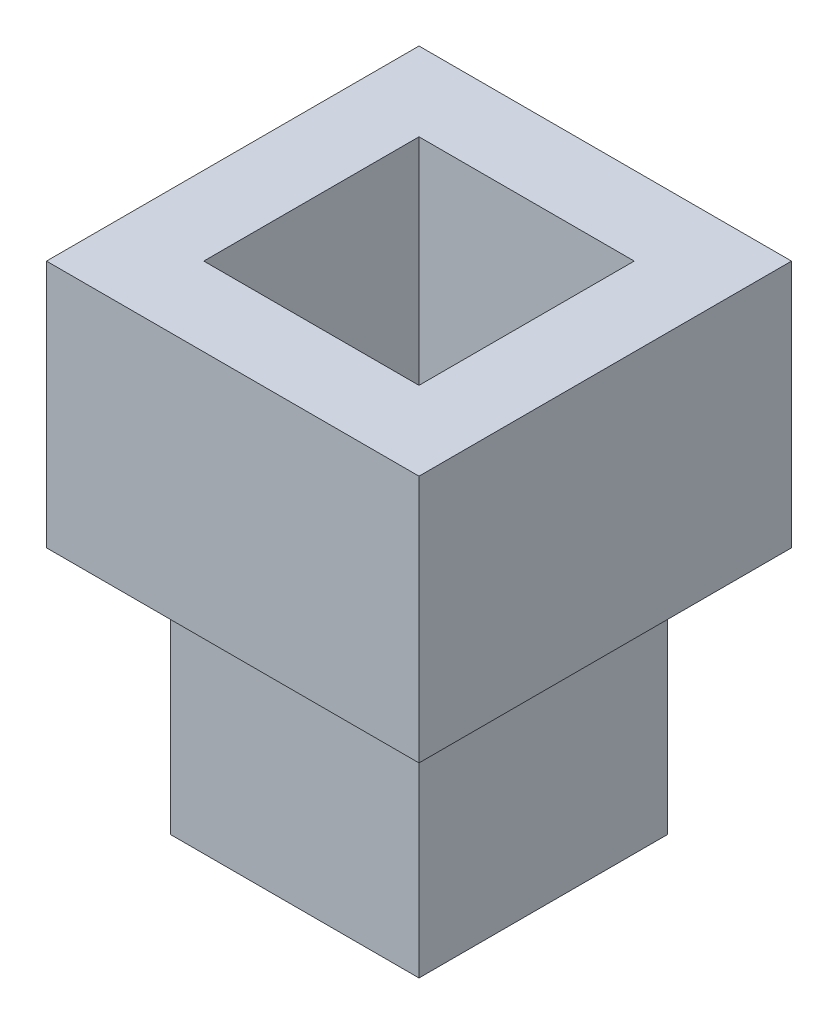
SolidWorks part; units mm, degrees
ref_plane "Front Plane" through (0, 0, 0) normal (0, 0, 1) x (1, 0, 0)
ref_plane "Top Plane" through (0, 0, 0) normal (0, 1, 0) x (1, 0, 0)
ref_plane "Right Plane" through (0, 0, 0) normal (1, 0, 0) x (0, 0, -1)
sketch "Sketch1" plane through (0, 0, 0) normal (0, 1, 0) x (1, 0, 0)
  line L1 (0, 0) -> (30, 0)
  line L2 (0, 0) -> (0, 30)
  line L3 (0, 30) -> (30, 30)
  line L4 (30, 0) -> (30, 30)
  dimension "D1" = 30
  dimension "D2" = 30
extrude "Boss-Extrude1" add sketch "Sketch1" along normal blind 30
sketch "Sketch2" plane through (0, 30, 0) normal (0, 1, 0) x (1, 0, 0)
  line L1 (-7.5, 37.5) -> (37.5, 37.5)
  line L2 (-7.5, 37.5) -> (-7.5, -7.5)
  line L3 (-7.5, -7.5) -> (37.5, -7.5)
  line L4 (37.5, 37.5) -> (37.5, -7.5)
  dimension "D1" = 45
  dimension "D2" = 45
  dimension "D3" = 7.5
  dimension "D4" = 7.5
extrude "Boss-Extrude2" add sketch "Sketch2" along normal blind 10
sketch "Sketch4" plane through (0, 40, 0) normal (0, 1, 0) x (1, 0, 0)
  line L1 (-7.5, 37.5) -> (37.5, 37.5)
  line L2 (-7.5, 37.5) -> (-7.5, -7.5)
  line L3 (-7.5, -7.5) -> (37.5, -7.5)
  line L4 (37.5, 37.5) -> (37.5, -7.5)
extrude "Boss-Extrude3" add sketch "Sketch4" along normal blind 20
sketch "Sketch5" plane through (0, 60, 0) normal (0, 1, 0) x (1, 0, 0)
  circle A0 centre (15, 15) radius 9.5
  dimension "D1" = 19
extrude "Cut-Extrude1" cut sketch "Sketch5" against normal blind 40
sketch "Sketch6" plane through (0, 60, 0) normal (0, 1, 0) x (1, 0, 0)
  line L0 (-7.5, 37.5) -> (-7.5, -7.5) construction
  line L1 (2, 2) -> (28, 2)
  line L2 (2, 2) -> (2, 28)
  line L3 (2, 28) -> (28, 28)
  line L4 (28, 2) -> (28, 28)
  line L5 (-7.5, -7.5) -> (37.5, -7.5) construction
  point P6 (-7.5, 15)
  point P7 (2, 15)
  point P10 (15, -7.5)
  point P11 (15, 2)
  dimension "D1" = 26
  dimension "D2" = 26
  dimension "D3" = 0
  dimension "D4" = 0
extrude "Cut-Extrude2" cut sketch "Sketch6" against normal blind 30
sketch "Sketch7" plane through (0, 0, 0) normal (0, -1, 0) x (1, 0, 0)
  line L0 (30, -30) -> (0, -30) construction
  line L1 (30, 0) -> (30, -30) construction
  line L2 (0, -30) -> (0, 0) construction
  line L3 (0, 0) -> (30, 0) construction
  circle A0 centre (25, -25) radius 2.5
  circle A1 centre (5, -25) radius 2.5
  circle A2 centre (5, -5) radius 2.5
  circle A3 centre (25, -5) radius 2.5
  dimension "D1" = 5
  dimension "D4" = 5
  dimension "D6" = 5
  dimension "D8" = 5
  dimension "D2" = 5
  dimension "D3" = 5
  dimension "D5" = 5
  dimension "D7" = 5
extrude "Cut-Extrude3" cut sketch "Sketch7" against normal blind 20
